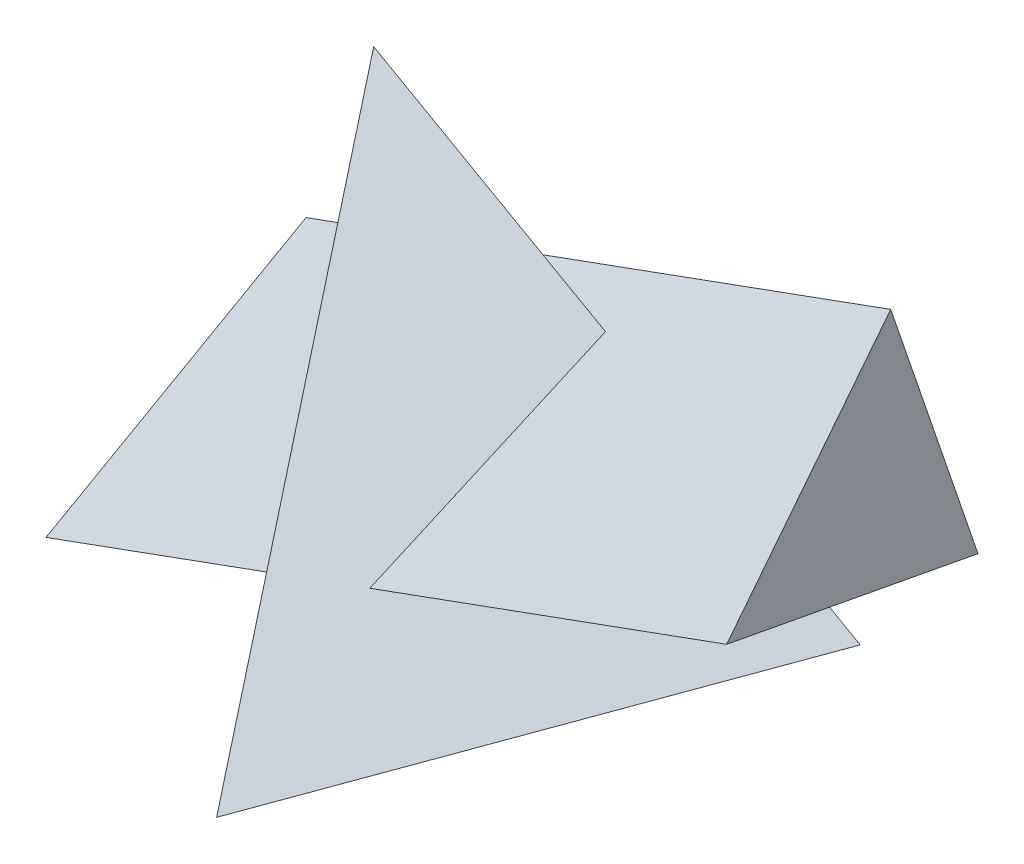
SolidWorks part; units mm, degrees
ref_plane "VP" through (0, 0, 0) normal (0, 0, 1) x (1, 0, 0)
ref_plane "HP" through (0, 0, 0) normal (0, 1, 0) x (1, 0, 0)
ref_plane "Right Plane" through (0, 0, 0) normal (1, 0, 0) x (0, 0, -1)
sketch "Edge of pyramid on HP" plane through (0, 0, 0) normal (0, 1, 0) x (1, 0, 0)
  line L0 (75, 30) -> (75, -90) construction
  line L1 (0, -55) -> (0, 55) construction
  line L2 (-38.1543, 0) -> (38.1543, 0) construction
  dimension "D1" = 75
  dimension "D2" = 30
  dimension "D3" = 120
ref_plane "Mid-plane on pyramid" through (0, 0, 30) normal (0, 0, 1) x (1, 0, 0)
sketch "triangle" plane through (0, 0, 30) normal (0, 0, 1) x (1, 0, 0)
  line L0 (31.4772, 0) -> (-31.4772, 0) construction
  point P0 (55, 130)
  dimension "D1" = 130
  dimension "D2" = 20
sketch "location of triangle points" plane through (0, 0, 30) normal (0, 0, 1) x (1, 0, 0)
  line L0 (75, 0) -> (178.923, 60) construction
  line L1 (31.4772, 0) -> (-31.4772, 0) construction
  dimension "D1" = 30
  dimension "D2" = 60
ref_plane "Base of pyramid" through (18.75, -32.476, 0) normal (0.5, -0.866, 0) x (-0.866, -0.5, 0)
sketch "point" plane through (18.75, -32.476, 0) normal (0.5, -0.866, 0) x (-0.866, -0.5, 0)
  line L0 (-184.9519, -30) -> (-64.9519, 30)
  line L1 (-64.9519, 30) -> (-64.9519, -90)
  line L2 (-64.9519, -90) -> (-184.9519, -30)
loft "Pyramid" add profiles "point", "triangle"
sketch "Projection of triangle" plane through (0, 0, 0) normal (0, 0, 1) x (1, 0, 0)
  line L0 (0, 0) -> (360.3695, 131.1638) construction
  line L1 (31.4772, 0) -> (-31.4772, 0) construction
  line L2 (263.9292, 96.0624) -> (263.9292, 161.0624)
  line L3 (263.9292, 161.0624) -> (320.2208, 128.5624)
  line L4 (320.2208, 128.5624) -> (263.9292, 96.0624)
  line L5 (320.2208, 128.5624) -> (0, 12.0115) construction
  line L6 (0, -66.0001) -> (0, 66.0001) construction
  line L7 (263.9292, 161.0624) -> (0, 65) construction
  line L8 (263.9292, 161.0624) -> (284.8198, 103.6659) construction
  line L9 (320.2208, 128.5624) -> (324.0813, 117.9559) construction
  dimension "D1" = 20
  dimension "D2" = 65
  dimension "D3" = 30
  dimension "D5" = 22.2313
  dimension "D6" = 41.7812
ref_plane "End plane RHS" through (178.923, 0, 0) normal (1, 0, 0) x (0, 0, -1)
sketch "Sketch10" plane through (178.923, 0, 0) normal (1, 0, 0) x (0, 0, -1)
  line L0 (0, 65.1227) -> (-22.2313, 130.1227)
  line L1 (-22.2313, 130.1227) -> (-64.0125, 77.1342)
  line L2 (-64.0125, 77.1342) -> (0, 65.1227)
  line L6 (0, 130.1227) -> (-88.2136, 130.1227) construction
  line L14 (-113.2835, 77.1342) -> (0, 77.1342) construction
  dimension "D1" = 22.2313
  dimension "D2" = 41.7812
sketch "Sketch11" plane through (0, 0, 0) normal (0, 0, 1) x (1, 0, 0)
  line L0 (0, 0) -> (178.923, 65.1227)
sweep "Triangular prism" add profiles "Sketch10" path "Sketch11"
sketch "Sketch8" plane through (0, 0, 0) normal (0, 0, 1) x (1, 0, 0)
  line L0 (0, 0) -> (30, 75.9191)
  line L2 (30, 75.9191) -> (0, 75.9191)
  line L3 (0, -66.0001) -> (0, 66.0001) construction
  line L4 (0, 75.9191) -> (0, 0)
  line L5 (263.9292, 161.0624) -> (0, 65) construction
  dimension "D1" = 30
extrude "Cut on LHS of prism" cut sketch "Sketch8" along normal through all
equation "\"D2\"= \"D6@Projection of triangle\""
equation "\"D1\"= \"D5@Projection of triangle\""
equation "\"D1@Sketch10\"=\"D1\""
equation "\"D2@Sketch10\"=\"D2\""
